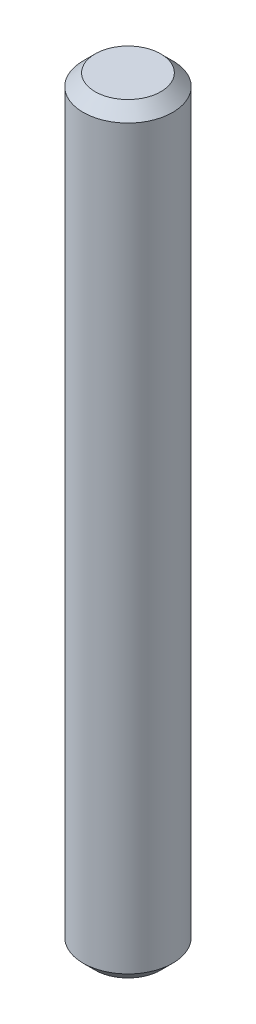
SolidWorks part; units mm, degrees
material "Stainless Steel (ferritic)"
ref_plane "Front Plane" through (0, 0, 0) normal (0, 0, 1) x (1, 0, 0)
ref_plane "Top Plane" through (0, 0, 0) normal (0, 1, 0) x (1, 0, 0)
ref_plane "Right Plane" through (0, 0, 0) normal (1, 0, 0) x (0, 0, -1)
sketch "Sketch1" plane through (0, 0, 0) normal (0, 1, 0) x (1, 0, 0)
  circle A0 centre (0, 0) radius 1.5
  dimension "D1" = 3
extrude "Boss-Extrude1" add sketch "Sketch1" along normal mid plane 25.5
chamfer "Chamfer1" distance 0.4 angle 45 2 edges at (0, -12.75, 1.5) (0, 12.75, 1.5)
